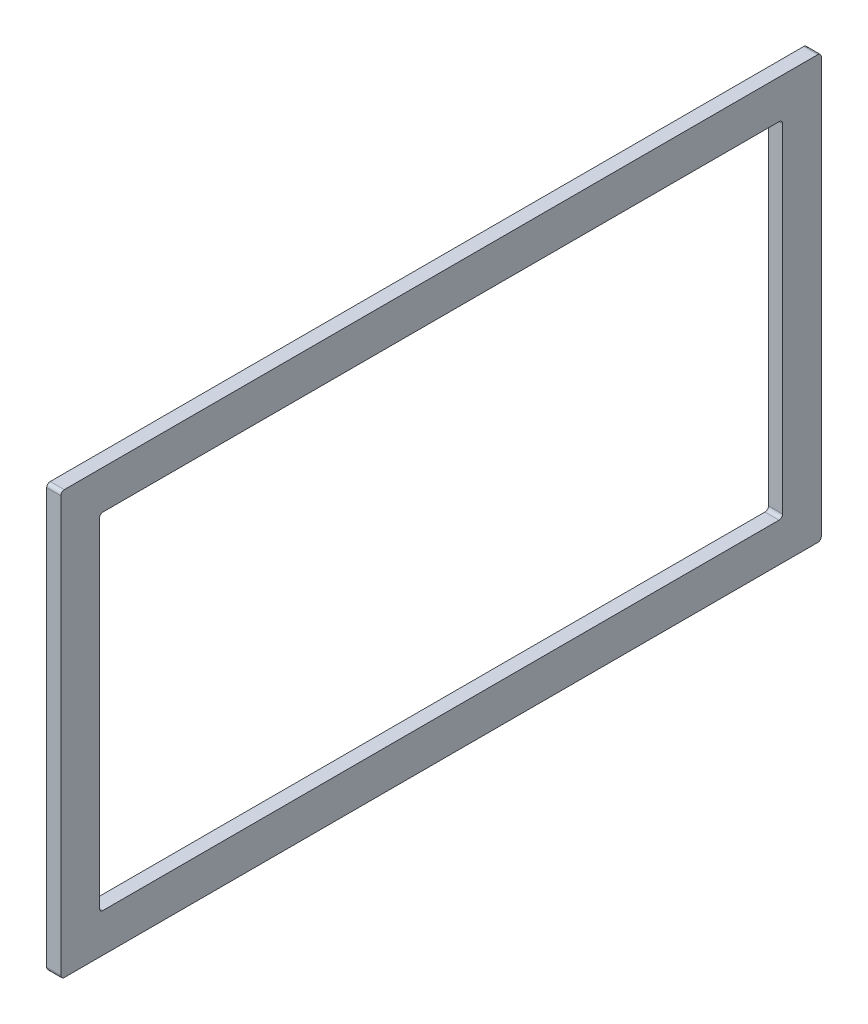
SolidWorks part; units mm, degrees
material "Rubber"
ref_plane "Front Plane" through (0, 0, 0) normal (0, 0, 1) x (1, 0, 0)
ref_plane "Top Plane" through (0, 0, 0) normal (0, 1, 0) x (1, 0, 0)
ref_plane "Right Plane" through (0, 0, 0) normal (1, 0, 0) x (0, 0, -1)
sketch "Sketch1" plane through (-311.15, 0, 0) normal (-1, 0, 0) x (0, 0, 1)
  line L1 (-342.9, 520.7) -> (342.9, 520.7)
  line L2 (-342.9, 520.7) -> (-342.9, 139.7)
  line L3 (-342.9, 139.7) -> (342.9, 139.7)
  line L4 (342.9, 520.7) -> (342.9, 139.7)
  line L5 (-307.975, 485.775) -> (307.975, 485.775)
  line L6 (-307.975, 485.775) -> (-307.975, 174.625)
  line L7 (-307.975, 174.625) -> (307.975, 174.625)
  line L8 (307.975, 485.775) -> (307.975, 174.625)
extrude "Boss-Extrude1" add sketch "Sketch1" along normal blind 12.7
fillet "Fillet1" radius 3.175 8 edges at (-317.5, 174.625, 307.975) (-317.5, 485.775, 307.975) (-317.5, 174.625, -307.975) (-317.5, 520.7, -342.9) (-317.5, 520.7, 342.9) (-317.5, 139.7, 342.9) (-317.5, 139.7, -342.9) (-317.5, 485.775, -307.975)
